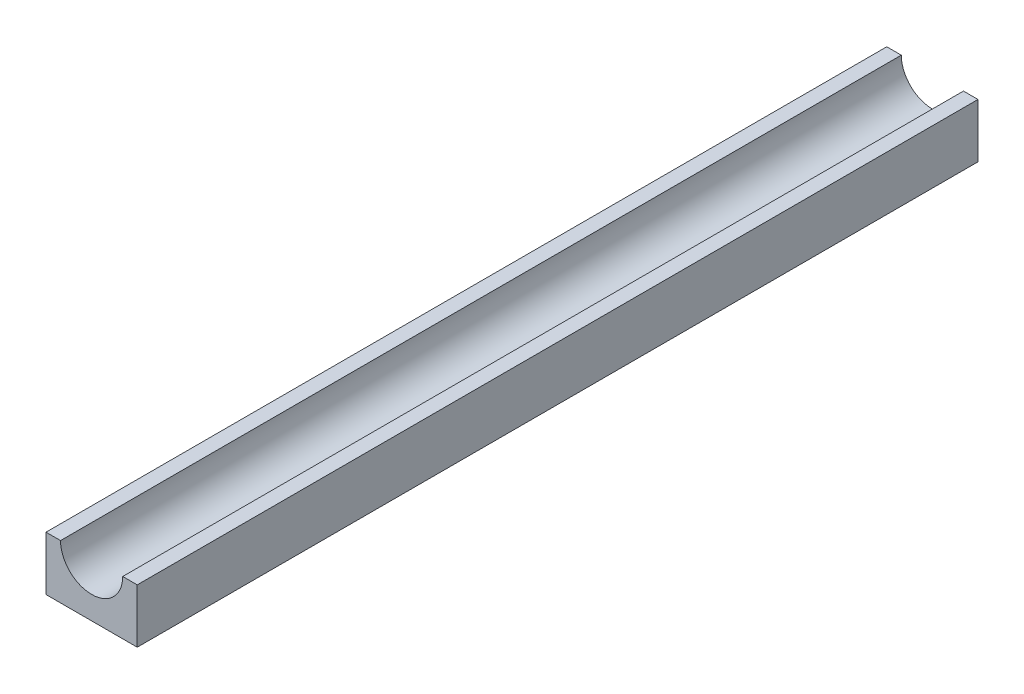
SolidWorks part; units mm, degrees
ref_plane "Front Plane" through (0, 0, 0) normal (0, 0, 1) x (1, 0, 0)
ref_plane "Top Plane" through (0, 0, 0) normal (0, 1, 0) x (1, 0, 0)
ref_plane "Right Plane" through (0, 0, 0) normal (1, 0, 0) x (0, 0, -1)
sketch "Sketch1" plane through (0, 0, 0) normal (0, 0, 1) x (1, 0, 0)
  line L0 (8.1375, 7.0688) -> (11.9375, 7.0688)
  line L1 (-11.9375, -7.0688) -> (11.9375, -7.0688)
  line L2 (-11.9375, -7.0688) -> (-11.9375, 7.0688)
  line L3 (-11.9375, 7.0688) -> (-8.1375, 7.0688)
  line L4 (11.9375, -7.0688) -> (11.9375, 7.0688)
  line L5 (-11.9375, -7.0688) -> (11.9375, 7.0688) construction
  line L6 (-11.9375, 7.0688) -> (11.9375, -7.0688) construction
  line L7 (-8.1375, 7.0688) -> (8.1375, 7.0688) construction
  arc A0 (-7.9375, 7.0688) -> (7.9375, 7.0688) centre (0, 7.0688) ccw construction
  arc A1 (-8.1375, 7.0688) -> (8.1375, 7.0688) centre (0, 7.0688) ccw
  point P0 (0, 0)
  point P9 (0, -4.3465)
  point P10 (0, 0)
  point P11 (0, -3.3932)
  point P12 (0, -1.0687)
  point P15 (0, 0)
  dimension "D1" = 7.9375
  dimension "D3" = 4
  dimension "D4" = 6
  dimension "D2" = 0.2
extrude "Boss-Extrude1" add sketch "Sketch1" along normal blind 220 contours A1 L0 L4 L1 L2 L3
equation "\"Rod diameter\"= 0.625in'Diameter of mandrel rod"
equation "\"Rod radius\"= \"Rod diameter\" / 2'Calculated radius of mandrel rod"
equation "\"Tape spring thickness\"= 0.4mm'Thickness of the tape spring"
equation "\"Tape spring length\" = 22cm"
equation "\"D2@Sketch1\"=\"Tape spring thickness\"*0.5"
equation "\"D1@Boss-Extrude1\"=\"Tape spring length\""
equation "\"D1@Sketch1\"=\"Rod radius\""
